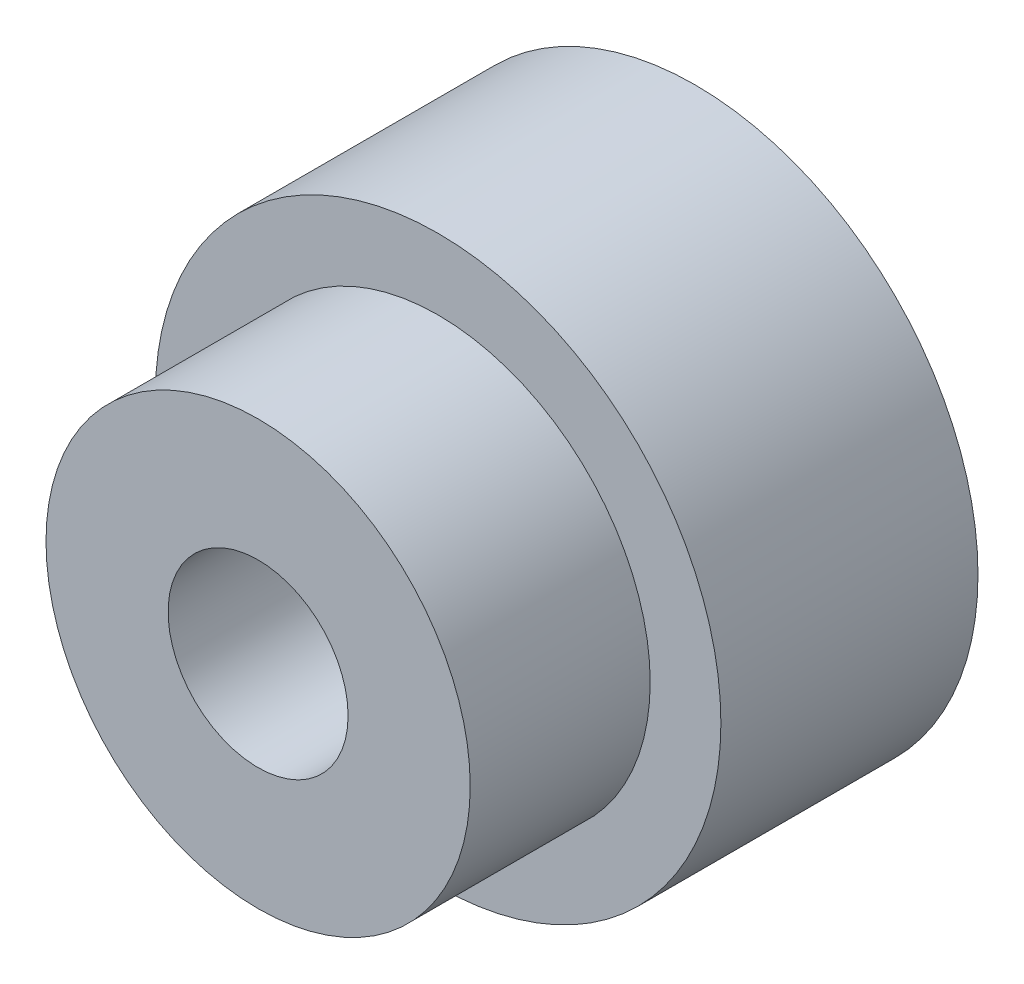
SolidWorks part; units mm, degrees
ref_plane "前视基准面" through (0, 0, 0) normal (0, 0, 1) x (1, 0, 0)
ref_plane "上视基准面" through (0, 0, 0) normal (0, 1, 0) x (1, 0, 0)
ref_plane "右视基准面" through (0, 0, 0) normal (1, 0, 0) x (0, 0, -1)
sketch "草图1" plane through (0, 0, 0) normal (0, 0, 1) x (1, 0, 0)
  circle A0 centre (0, 0) radius 22
  dimension "D1" = 44
extrude "凸台-拉伸1" add sketch "草图1" along normal blind 20
sketch "草图3" plane through (0, 0, 20) normal (0, 0, 1) x (1, 0, 0)
  circle A0 centre (0, 0) radius 16.5
  dimension "D1" = 33
extrude "凸台-拉伸2" add sketch "草图3" along normal blind 14
sketch "草图5" plane through (0, 0, 34) normal (0, 0, 1) x (1, 0, 0)
  circle A0 centre (0, 0) radius 7
  dimension "D1" = 14
extrude "切除-拉伸3" cut sketch "草图5" against normal blind 94.8
